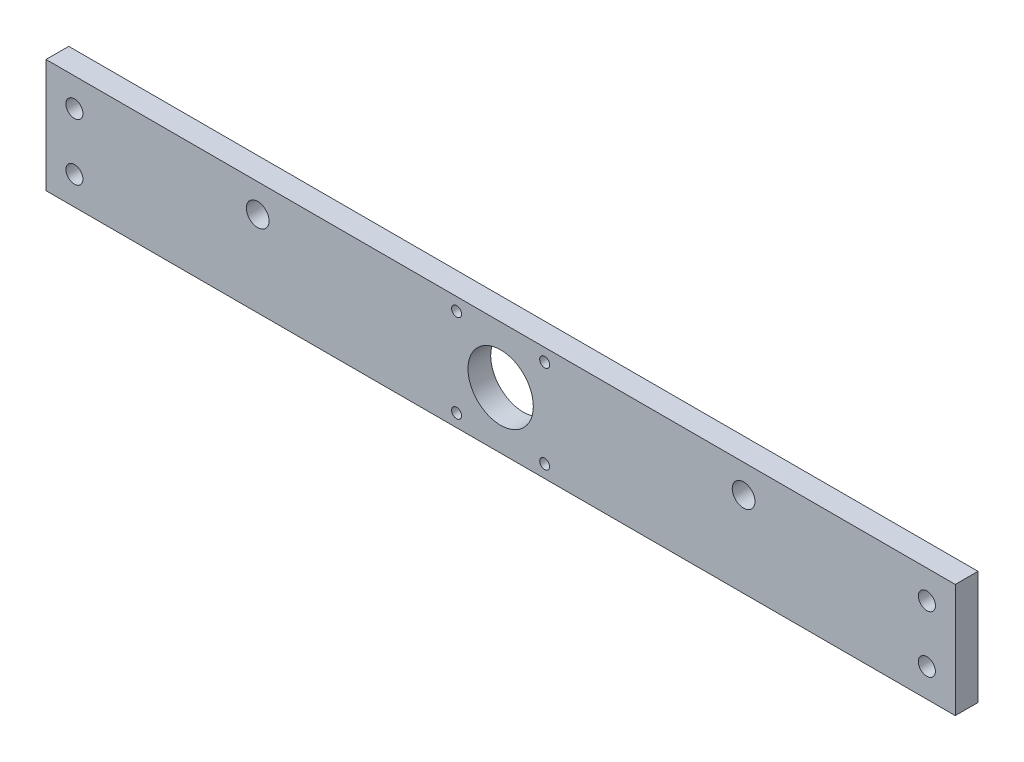
SolidWorks part; units mm, degrees
ref_plane "Front Plane" through (0, 0, 0) normal (0, 0, 1) x (1, 0, 0)
ref_plane "Top Plane" through (0, 0, 0) normal (0, 1, 0) x (1, 0, 0)
ref_plane "Right Plane" through (0, 0, 0) normal (1, 0, 0) x (0, 0, -1)
sketch "Sketch1" plane through (0, 0, 0) normal (0, 0, 1) x (1, 0, 0)
  line L1 (-160, -20) -> (160, -20)
  line L2 (-160, -20) -> (-160, 20)
  line L3 (-160, 20) -> (160, 20)
  line L4 (160, -20) -> (160, 20)
  line L5 (-160, -20) -> (160, 20) construction
  line L6 (-160, 20) -> (160, -20) construction
  point P0 (0, 0)
  dimension "D1" = 320
  dimension "D2" = 40
extrude "Boss-Extrude1" add sketch "Sketch1" along normal blind 8
sketch "Sketch2" plane through (0, 0, 8) normal (0, 0, 1) x (1, 0, 0)
  line L0 (0, 20) -> (0, -20) construction
  line L1 (160, 20) -> (-160, 20) construction
  line L2 (-160, -20) -> (160, -20) construction
  line L3 (-160, 0) -> (160, 0) construction
  line L4 (-160, 20) -> (-160, -20) construction
  line L5 (160, -20) -> (160, 20) construction
  circle A0 centre (-150, 10) radius 3
  circle A1 centre (-150, -10) radius 3
  circle A2 centre (150, -10) radius 3
  circle A3 centre (150, 10) radius 3
  dimension "D1" = 10
  dimension "D2" = 10
  dimension "D3" = 6
extrude "Cut-Extrude1" cut sketch "Sketch2" against normal up to next
sketch "Sketch3" plane through (0, 0, 8) normal (0, 0, 1) x (1, 0, 0)
  line L0 (0, 20) -> (0, -20) construction
  line L1 (160, 20) -> (-160, 20) construction
  line L2 (-160, -20) -> (160, -20) construction
  line L3 (-150, 10) -> (150, 10) construction
  circle A0 centre (-85.5, 10) radius 4
  circle A1 centre (85.5, 10) radius 4
  circle A2 centre (0, 0) radius 11.5
  dimension "D1" = 8
  dimension "D2" = 85.5
  dimension "D3" = 23
extrude "Cut-Extrude2" cut sketch "Sketch3" against normal up to next
sketch "Sketch4" plane through (0, 0, 8) normal (0, 0, 1) x (1, 0, 0)
  line L0 (0, 0) -> (-20, 20) construction
  line L1 (160, 20) -> (-160, 20) construction
  line L2 (0, 20) -> (0, -20) construction
  line L3 (-160, -20) -> (160, -20) construction
  line L4 (0, 0) -> (-160, 0) construction
  line L5 (-160, 20) -> (-160, -20) construction
  circle A0 centre (-15.5, 15.5) radius 1.75
  circle A1 centre (15.5, 15.5) radius 1.75
  circle A2 centre (-15.5, -15.5) radius 1.75
  circle A3 centre (15.5, -15.5) radius 1.75
  dimension "D2" = 3.5
  dimension "D3" = 15.5
  dimension "D1" = 45
extrude "Cut-Extrude3" cut sketch "Sketch4" against normal up to next
